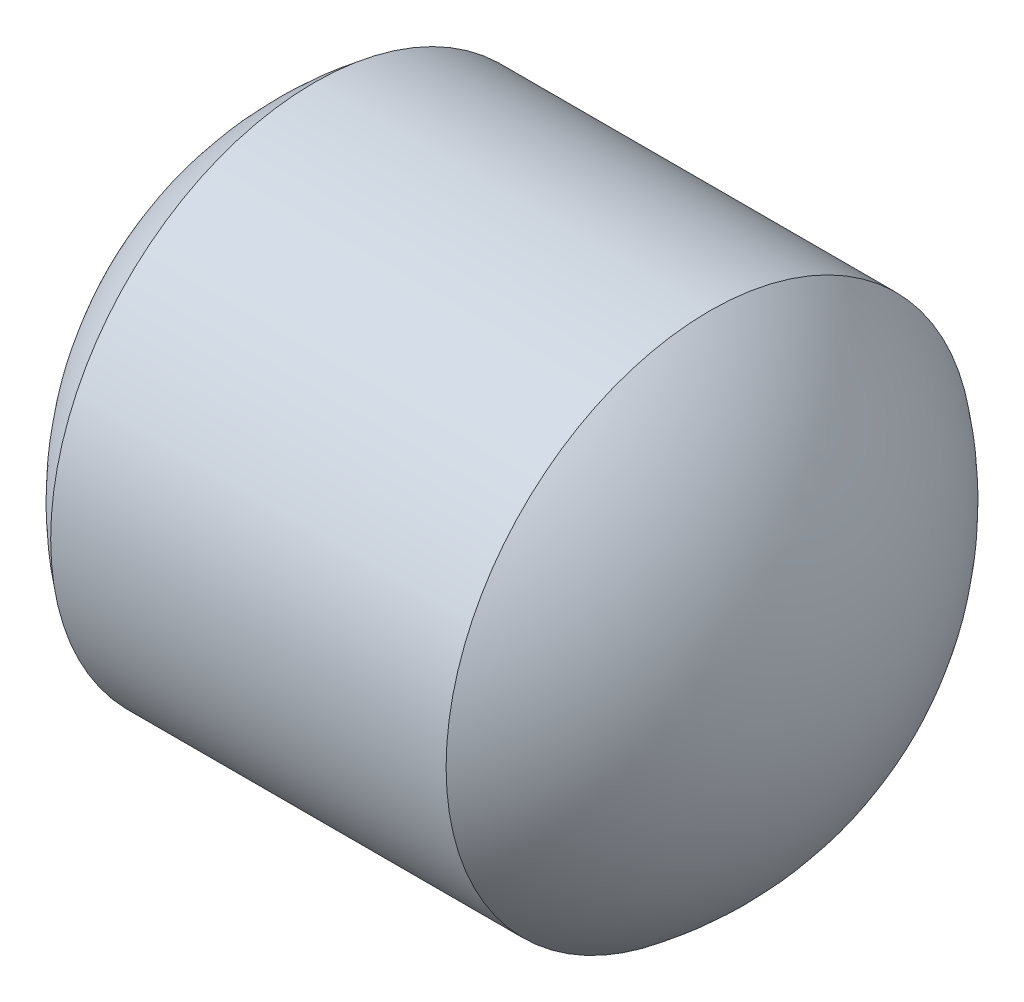
SolidWorks part; units mm, degrees
ref_plane "前视基准面" through (0, 0, 0) normal (0, 0, 1) x (1, 0, 0)
ref_plane "上视基准面" through (0, 0, 0) normal (0, 1, 0) x (1, 0, 0)
ref_plane "右视基准面" through (0, 0, 0) normal (1, 0, 0) x (0, 0, -1)
sketch "草图1" plane through (0, 0, 0) normal (0, 0, 1) x (1, 0, 0)
  line L0 (3431.4545, 1943.1954) -> (3431.4545, 1939.1962)
  line L1 (3434.4539, 1943.1954) -> (3434.4539, 1939.1962)
  line L2 (3431.4545, 1943.1954) -> (3434.4539, 1943.1954)
  line L3 (3431.4545, 1939.1962) -> (3434.4539, 1939.1962)
  line L4 (3430.0322, 1941.1958) -> (3436.0425, 1941.1958) construction
  arc A0 (3431.4545, 1943.1954) -> (3431.4545, 1939.1962) centre (3432.9542, 1941.1958) ccw
  arc A1 (3434.4539, 1939.1962) -> (3434.4539, 1943.1954) centre (3432.9542, 1941.1958) ccw
revolve "旋转1" add sketch "草图1" angle 360 about L4
